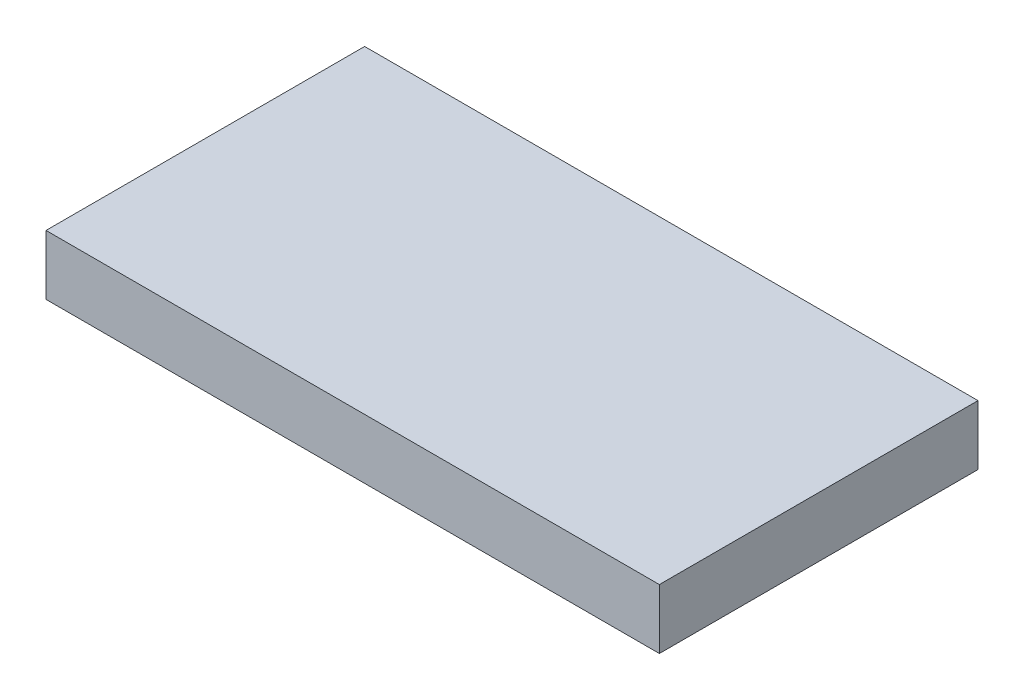
SolidWorks part; units mm, degrees
ref_plane "Front Plane" through (0, 0, 0) normal (0, 0, 1) x (1, 0, 0)
ref_plane "Top Plane" through (0, 0, 0) normal (0, 1, 0) x (1, 0, 0)
ref_plane "Right Plane" through (0, 0, 0) normal (1, 0, 0) x (0, 0, -1)
sketch "Sketch1" plane through (0, 0, 0) normal (0, 1, 0) x (1, 0, 0)
  line L1 (-0.77, -0.4) -> (0.77, -0.4)
  line L2 (-0.77, -0.4) -> (-0.77, 0.4)
  line L3 (-0.77, 0.4) -> (0.77, 0.4)
  line L4 (0.77, -0.4) -> (0.77, 0.4)
  line L5 (-0.77, -0.4) -> (0.77, 0.4) construction
  line L6 (-0.77, 0.4) -> (0.77, -0.4) construction
  point P0 (0, 0)
  dimension "D1" = 1.54
  dimension "D2" = 0.8
extrude "Boss-Extrude1" add sketch "Sketch1" along normal blind 0.15
